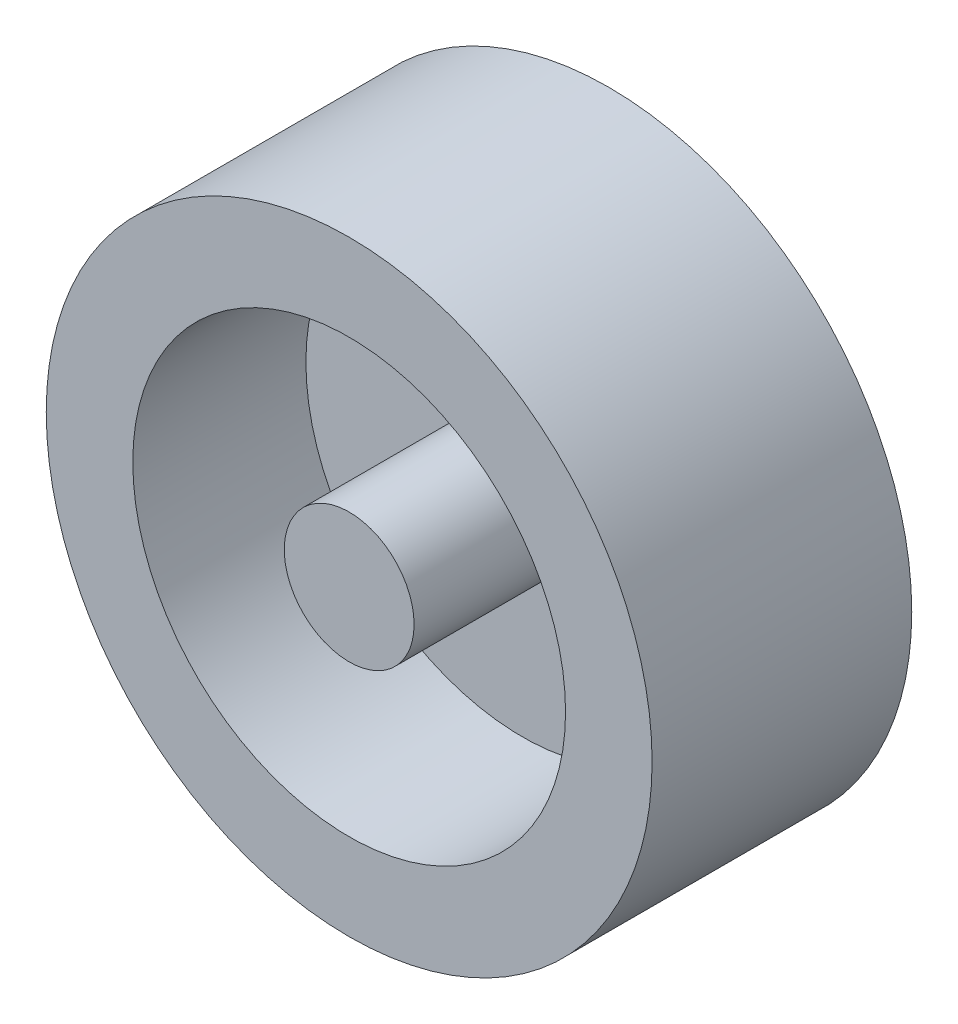
SolidWorks part; units mm, degrees
ref_plane "Alzado" through (0, 0, 0) normal (0, 0, 1) x (1, 0, 0)
ref_plane "Planta" through (0, 0, 0) normal (0, 1, 0) x (1, 0, 0)
ref_plane "Vista lateral" through (0, 0, 0) normal (1, 0, 0) x (0, 0, -1)
sketch "Croquis1" plane through (0, 0, 0) normal (0, 0, 1) x (1, 0, 0)
  circle A0 centre (0, 0) radius 3.5
  dimension "D1" = 7
extrude "Saliente-Extruir1" add sketch "Croquis1" along normal blind 3
sketch "Croquis2" plane through (0, 0, 3) normal (0, 0, 1) x (1, 0, 0)
  circle A0 centre (0, 0) radius 2.5
  dimension "D1" = 5
extrude "Cortar-Extruir1" cut sketch "Croquis2" against normal blind 2
sketch "Croquis3" plane through (0, 0, 1) normal (0, 0, 1) x (1, 0, 0)
  circle A0 centre (0, 0) radius 0.75
  dimension "D1" = 1.5
extrude "Saliente-Extruir2" add sketch "Croquis3" along normal blind 2
